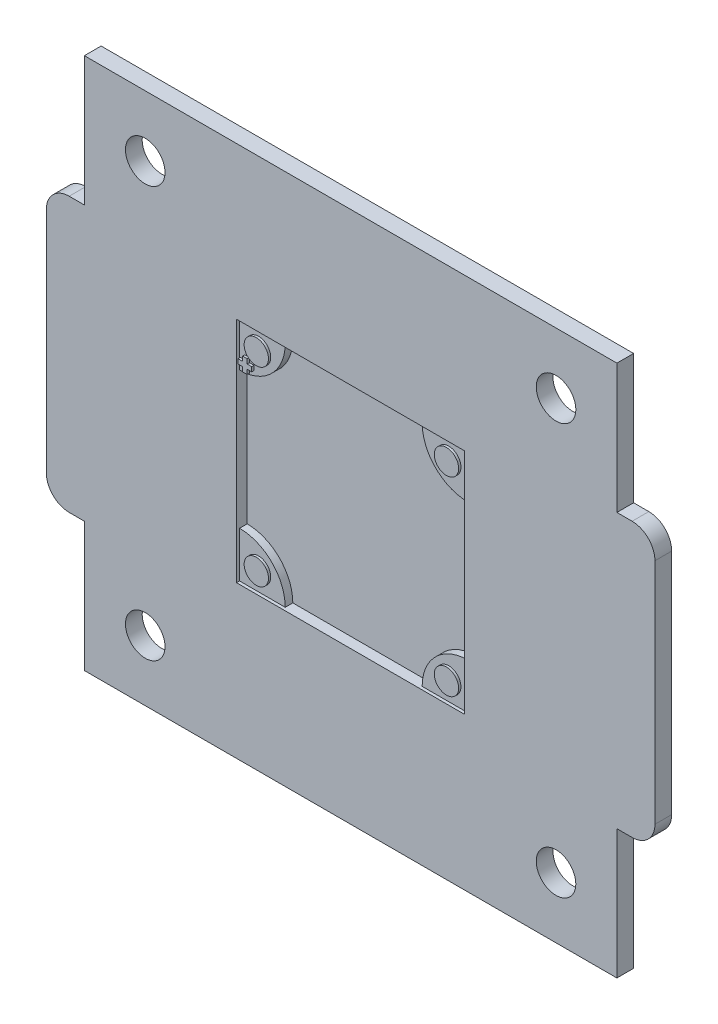
SolidWorks part; units mm, degrees
ref_plane "前视基准面" through (0, 0, 0) normal (0, 0, 1) x (1, 0, 0)
ref_plane "上视基准面" through (0, 0, 0) normal (0, 1, 0) x (1, 0, 0)
ref_plane "右视基准面" through (0, 0, 0) normal (1, 0, 0) x (0, 0, -1)
sketch "草图1" plane through (0, 0, 0) normal (0, 0, 1) x (1, 0, 0)
  line L0 (35, 70) -> (35, 0) construction
  line L1 (0, 0) -> (70, 0)
  line L2 (0, 0) -> (0, 70)
  line L3 (0, 70) -> (70, 70)
  line L4 (70, 0) -> (70, 70)
  line L5 (0, 35) -> (70, 35) construction
  line L6 (70, 17) -> (72, 17)
  line L7 (0, 53) -> (-2, 53)
  line L8 (0, 53) -> (0, 17)
  line L9 (0, 17) -> (-2, 17)
  line L10 (-5, 50) -> (-5, 20)
  line L11 (75, 50) -> (75, 20)
  line L12 (70, 53) -> (72, 53)
  line L13 (70, 53) -> (70, 17)
  arc A0 (-2, 17) -> (-5, 20) centre (-2, 20) cw
  arc A1 (-2, 53) -> (-5, 50) centre (-2, 50) ccw
  arc A2 (72, 17) -> (75, 20) centre (72, 20) ccw
  arc A3 (72, 53) -> (75, 50) centre (72, 50) cw
  point P6 (35, 70)
  point P10 (0, 35)
  point P15 (-5, 35)
  point P18 (-5, 17)
  point P21 (-5, 53)
  dimension "D4" = 3
  dimension "D1" = 70
  dimension "D2" = 5
  dimension "D3" = 36
extrude "凸台-拉伸1" add sketch "草图1" along normal blind 2.2 contours L7 A1 L10 A0 L9 L2 | L1 L4 L3 L2 | A3 L12 L4 L6 A2 L11
sketch "草图2" plane through (0, 0, 2.2) normal (0, 0, 1) x (1, 0, 0)
  line L0 (0, 70) -> (70, 70) construction
  line L1 (35, 70) -> (35, 0) construction
  line L2 (0, 0) -> (70, 0) construction
  line L3 (-5, 50) -> (-5, 20) construction
  line L4 (-5, 35) -> (75, 35) construction
  line L5 (75, 50) -> (75, 20) construction
  line L7 (20, 50) -> (50, 50)
  line L8 (20, 50) -> (20, 20)
  line L9 (20, 20) -> (50, 20)
  line L10 (50, 50) -> (50, 20)
  point P6 (35, 70)
  point P17 (35, 50)
  point P18 (20, 35)
  dimension "D1" = 30
extrude "切除-拉伸1" cut sketch "草图2" against normal blind 1.4
sketch "草图3" plane through (0, 0, 2.2) normal (0, 0, 1) x (1, 0, 0)
  line L0 (0, 70) -> (0, 0) construction
  line L1 (0, 70) -> (70, 70) construction
  line L2 (0, 53) -> (0, 70) construction
  line L3 (70, 0) -> (70, 70) construction
  line L4 (70, 53) -> (70, 70) construction
  line L5 (0, 35) -> (70, 35) construction
  line L6 (35, 70) -> (35, 0) construction
  line L7 (0, 0) -> (70, 0) construction
  circle A0 centre (8, 62) radius 2.6
  circle A1 centre (62, 62) radius 2.6
  circle A2 centre (8, 8) radius 2.6
  circle A3 centre (62, 8) radius 2.6
  point P18 (35, 70)
  point P19 (0, 35)
  dimension "D3" = 5.2
  dimension "D1" = 8
  dimension "D2" = 8
extrude "切除-拉伸2" cut sketch "草图3" against normal through all
sketch "草图4" plane through (0, 0, 0) normal (0, 0, 1) x (1, 0, 0)
  line L0 (20, 35) -> (50, 35) construction
  line L1 (20, 50) -> (50, 50) construction
  line L2 (20, 50) -> (20, 20) construction
  line L3 (20, 20) -> (50, 20) construction
  line L4 (50, 50) -> (50, 20) construction
  line L5 (35, 50) -> (35, 20) construction
  line L6 (20, 44) -> (20, 50)
  line L7 (20, 50) -> (26, 50)
  line L8 (50, 44) -> (50, 50)
  line L9 (50, 50) -> (44, 50)
  line L10 (50, 20) -> (44, 20)
  line L11 (50, 26) -> (50, 20)
  line L12 (20, 26) -> (20, 20)
  line L13 (20, 20) -> (26, 20)
  arc A0 (26, 50) -> (20, 44) centre (20, 50) cw
  arc A1 (44, 50) -> (50, 44) centre (50, 50) ccw
  arc A2 (44, 20) -> (50, 26) centre (50, 20) cw
  arc A3 (26, 20) -> (20, 26) centre (20, 20) ccw
  point P10 (35, 20)
  point P11 (20, 35)
  dimension "D1" = 6
extrude "凸台-拉伸2" add sketch "草图4" along normal blind 1.8
sketch "草图6" plane through (0, 0, 1.8) normal (0, 0, 1) x (1, 0, 0)
  line L0 (20, 35) -> (50, 35) construction
  line L1 (20, 50) -> (50, 50) construction
  line L2 (20, 50) -> (20, 20) construction
  line L3 (20, 20) -> (50, 20) construction
  line L4 (50, 50) -> (50, 20) construction
  line L5 (35, 50) -> (35, 20) construction
  line L6 (20.1, 45.5) -> (20.7, 45.5)
  line L7 (20.7, 45.5) -> (20.7, 46.1)
  line L8 (20.7, 46.1) -> (21.3, 46.1)
  line L9 (21.3, 46.1) -> (21.3, 45.5)
  line L10 (21.3, 45.5) -> (21.9, 45.5)
  line L11 (21.9, 45.5) -> (21.9, 44.9)
  line L12 (21.9, 44.9) -> (21.3, 44.9)
  line L13 (21.3, 44.9) -> (21.3, 44.3)
  line L14 (21.3, 44.3) -> (20.7, 44.3)
  line L15 (20.7, 44.3) -> (20.7, 44.9)
  line L16 (20.7, 44.9) -> (20.1, 44.9)
  line L17 (20.1, 44.9) -> (20.1, 45.5)
  circle A4 centre (22.5, 47.5) radius 1.6
  circle A5 centre (47.5, 47.5) radius 1.6
  circle A6 centre (47.5, 22.5) radius 1.6
  circle A7 centre (22.5, 22.5) radius 1.6
  point P10 (35, 20)
  point P11 (20, 35)
  point P31 (21, 46.1)
  dimension "D1" = 2.5
  dimension "D2" = 2.5
  dimension "D3" = 3.2
  dimension "D4" = 0.6
  dimension "D5" = 0.6
  dimension "D6" = 0.1
  dimension "D7" = 3.9
extrude "凸台-拉伸3" add sketch "草图6" along normal blind 0.3
